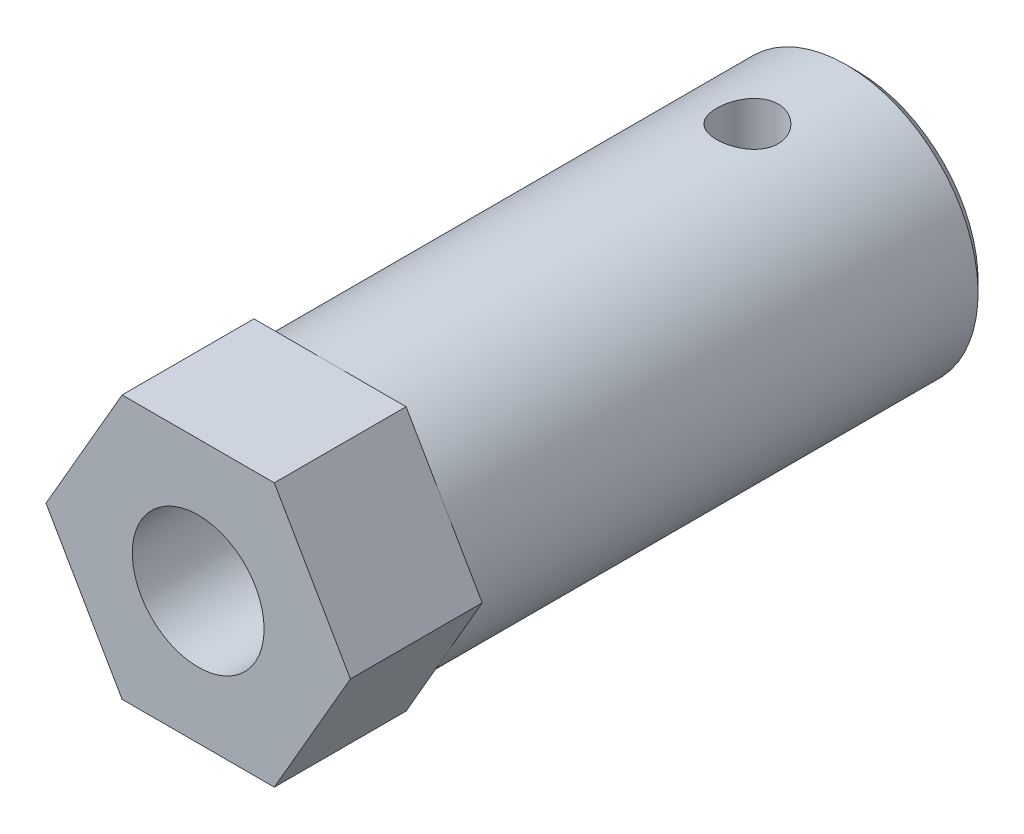
SolidWorks part; units mm, degrees
material "Bronze commercial au plomb"
ref_plane "Plan de face" through (0, 0, 0) normal (0, 0, 1) x (1, 0, 0)
ref_plane "Plan de dessus" through (0, 0, 0) normal (0, 1, 0) x (1, 0, 0)
ref_plane "Plan de droite" through (0, 0, 0) normal (1, 0, 0) x (0, 0, -1)
sketch "Esquisse1" plane through (0, 0, 0) normal (1, 0, 0) x (0, 0, -1)
  line L1 (0, 0) -> (-24, 0)
  line L2 (0, 0) -> (0, 6)
  line L3 (0, 6) -> (-24, 6)
  line L4 (-24, 0) -> (-24, 6)
  dimension "D1" = 24
  dimension "D2" = 6
revolve "Révolution1" add sketch "Esquisse1" angle 360 about L1
sketch "Esquisse2" plane through (0, 0, 24) normal (0, 0, 1) x (1, 0, 0)
  line L0 (6.9282, 0) -> (0, 0) construction
  line L1 (6.9282, 0) -> (3.4641, 6)
  line L2 (3.4641, 6) -> (-3.4641, 6)
  line L3 (-3.4641, 6) -> (-6.9282, 0)
  line L4 (-6.9282, 0) -> (-3.4641, -6)
  line L5 (-3.4641, -6) -> (3.4641, -6)
  line L6 (3.4641, -6) -> (6.9282, 0)
  circle A0 centre (0, 0) radius 6 construction
  dimension "D1" = 6
extrude "Boss.-Extru.1" add sketch "Esquisse2" along normal blind 6
sketch "Esquisse3" plane through (0, 0, 0) normal (0, 0, -1) x (-1, 0, 0)
  circle A0 centre (0, 0) radius 3
  dimension "D1" = 6
extrude "Enlèv. mat.-Extru.1" cut sketch "Esquisse3" against normal up to next
sketch "Esquisse4" plane through (0, 0, 0) normal (0, 1, 0) x (1, 0, 0)
  line L0 (0, 0) -> (0, -5) construction
  circle A1 centre (0, -5) radius 1.4009
  point P0 (0, -5)
  dimension "D1" = 5
extrude "Enlèv. mat.-Extru.2" cut sketch "Esquisse4" against normal through all both and the other way through all
chamfer "Chanfrein1" distance 0.5 angle 45 1 edges at (0, 6, 0)
